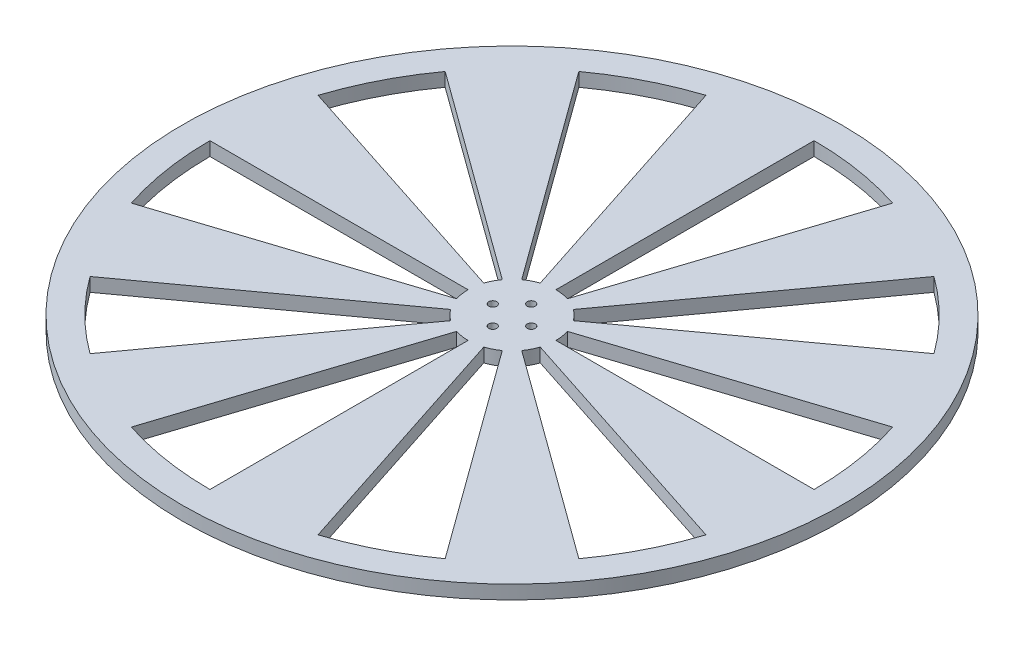
SolidWorks part; units mm, degrees
ref_plane "前视基准面" through (0, 0, 0) normal (0, 0, 1) x (1, 0, 0)
ref_plane "上视基准面" through (0, 0, 0) normal (0, 1, 0) x (1, 0, 0)
ref_plane "右视基准面" through (0, 0, 0) normal (1, 0, 0) x (0, 0, -1)
sketch "草图1" plane through (0, 0, 0) normal (0, 1, 0) x (1, 0, 0)
  line L0 (16, 0) -> (110, 0)
  line L1 (15.2169, 4.9443) -> (104.6162, 33.9919)
  line L2 (9.4046, 12.9443) -> (64.6564, 88.9919)
  line L3 (0, 16) -> (0, 110)
  line L4 (-9.4046, 12.9443) -> (-64.6564, 88.9919)
  line L5 (-15.2169, 4.9443) -> (-104.6162, 33.9919)
  line L6 (-15.2169, -4.9443) -> (-104.6162, -33.9919)
  line L7 (-9.4046, -12.9443) -> (-64.6564, -88.9919)
  line L8 (0, -16) -> (0, -110)
  line L9 (9.4046, -12.9443) -> (64.6564, -88.9919)
  line L10 (15.2169, -4.9443) -> (104.6162, -33.9919)
  line L11 (12.9443, 9.4046) -> (88.9919, 64.6564)
  line L12 (4.9443, 15.2169) -> (33.9919, 104.6162)
  line L13 (-4.9443, 15.2169) -> (-33.9919, 104.6162)
  line L14 (-12.9443, 9.4046) -> (-88.9919, 64.6564)
  line L15 (-16, 0) -> (-110, 0)
  line L16 (-12.9443, -9.4046) -> (-88.9919, -64.6564)
  line L17 (-4.9443, -15.2169) -> (-33.9919, -104.6162)
  line L18 (4.9443, -15.2169) -> (33.9919, -104.6162)
  line L19 (12.9443, -9.4046) -> (88.9919, -64.6564)
  circle A0 centre (0, 0) radius 120
  circle A1 centre (7, 0) radius 1.45
  circle A2 centre (0, 7) radius 1.45
  circle A3 centre (-7, 0) radius 1.45
  circle A4 centre (0, -7) radius 1.45
  arc A5 (110, 0) -> (104.6162, 33.9919) centre (0, 0) ccw
  arc A6 (88.9919, 64.6564) -> (64.6564, 88.9919) centre (0, 0) ccw
  arc A7 (33.9919, 104.6162) -> (0, 110) centre (0, 0) ccw
  arc A8 (-33.9919, 104.6162) -> (-64.6564, 88.9919) centre (0, 0) ccw
  arc A9 (-88.9919, 64.6564) -> (-104.6162, 33.9919) centre (0, 0) ccw
  arc A10 (-110, 0) -> (-104.6162, -33.9919) centre (0, 0) ccw
  arc A11 (-88.9919, -64.6564) -> (-64.6564, -88.9919) centre (0, 0) ccw
  arc A12 (-33.9919, -104.6162) -> (0, -110) centre (0, 0) ccw
  arc A13 (33.9919, -104.6162) -> (64.6564, -88.9919) centre (0, 0) ccw
  arc A14 (88.9919, -64.6564) -> (104.6162, -33.9919) centre (0, 0) ccw
  arc A15 (-12.9443, 9.4046) -> (-15.2169, 4.9443) centre (0, 0) ccw
  arc A16 (-16, 0) -> (-15.2169, -4.9443) centre (0, 0) ccw
  arc A17 (-12.9443, -9.4046) -> (-9.4046, -12.9443) centre (0, 0) ccw
  arc A18 (-4.9443, -15.2169) -> (0, -16) centre (0, 0) ccw
  arc A19 (4.9443, -15.2169) -> (9.4046, -12.9443) centre (0, 0) ccw
  arc A20 (12.9443, -9.4046) -> (15.2169, -4.9443) centre (0, 0) ccw
  arc A21 (16, 0) -> (15.2169, 4.9443) centre (0, 0) ccw
  arc A22 (12.9443, 9.4046) -> (9.4046, 12.9443) centre (0, 0) ccw
  arc A23 (4.9443, 15.2169) -> (0, 16) centre (0, 0) ccw
  arc A24 (-4.9443, 15.2169) -> (-9.4046, 12.9443) centre (0, 0) ccw
extrude "凸台-拉伸1" add sketch "草图1" along normal mid plane 5
